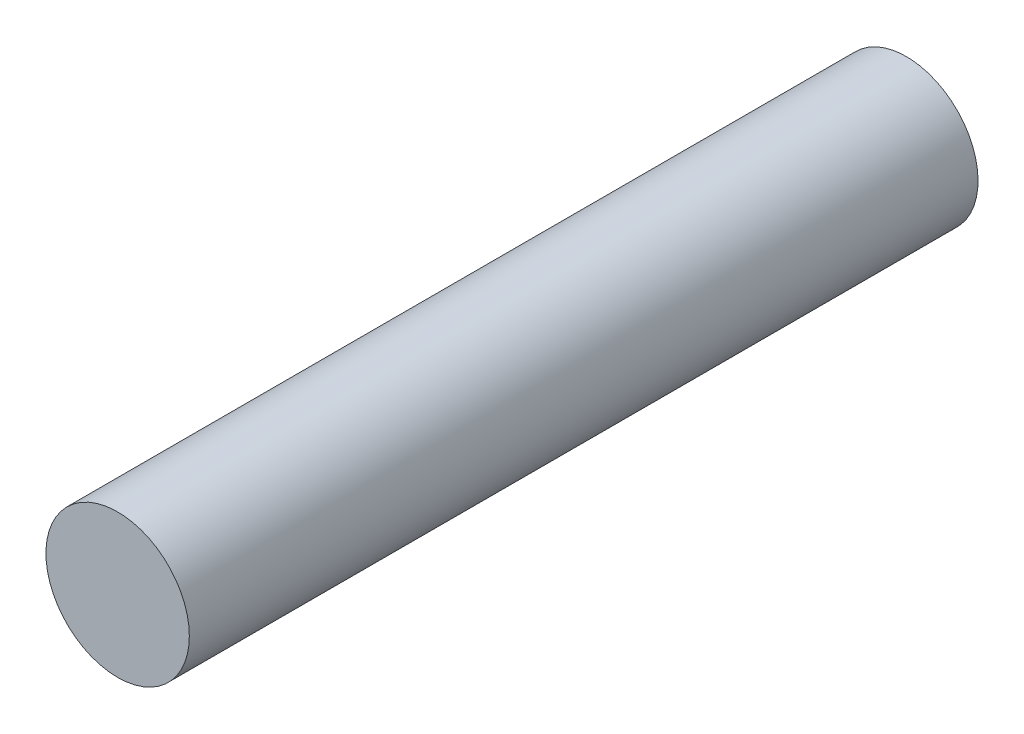
SolidWorks part; units mm, degrees
ref_plane "正面" through (0, 0, 0) normal (0, 0, 1) x (1, 0, 0)
ref_plane "平面" through (0, 0, 0) normal (0, 1, 0) x (1, 0, 0)
ref_plane "右側面" through (0, 0, 0) normal (1, 0, 0) x (0, 0, -1)
sketch "ｽｹｯﾁ1" plane through (0, 0, 0) normal (0, 0, 1) x (1, 0, 0)
  circle A0 centre (8, 30) radius 3 construction
  circle A1 centre (8, 30) radius 3
extrude "ﾎﾞｽ - 押し出し1" add sketch "ｽｹｯﾁ1" along normal up to surface (25 mm away) and the other way up to surface (8 mm away)
